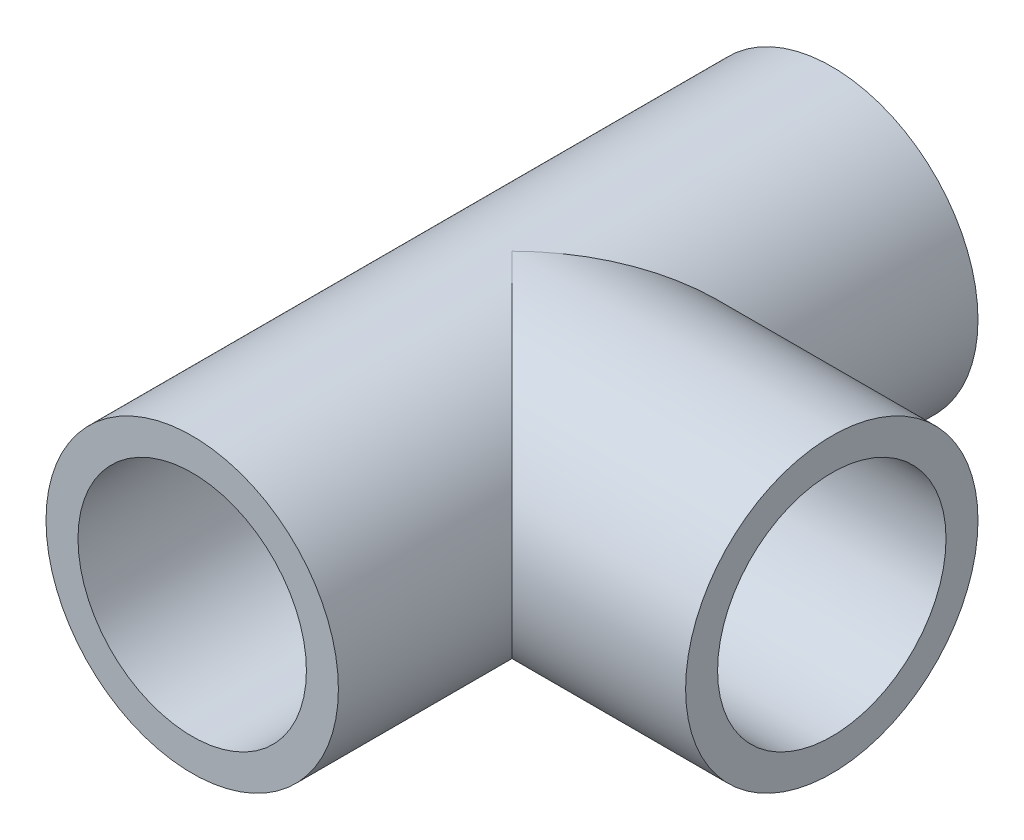
SolidWorks part; units mm, degrees
ref_plane "前视基准面" through (0, 0, 0) normal (0, 0, 1) x (1, 0, 0)
ref_plane "上视基准面" through (0, 0, 0) normal (0, 1, 0) x (1, 0, 0)
ref_plane "右视基准面" through (0, 0, 0) normal (1, 0, 0) x (0, 0, -1)
other "Configuration Table"
sketch "草图1" plane through (0, 0, 0) normal (0, 0, 1) x (1, 0, 0)
  circle A0 centre (0, 0) radius 12.5
  circle A1 centre (0, 0) radius 16
  dimension "D1" = 25
  dimension "D2" = 32
extrude "凸台-拉伸1" add sketch "草图1" along normal mid plane 70
sketch "草图2" plane through (0, 0, 0) normal (1, 0, 0) x (0, 0, -1)
  circle A0 centre (0, 0) radius 16
  circle A1 centre (0, 0) radius 12.5
  dimension "D1" = 32
  dimension "D2" = 25
extrude "凸台-拉伸2" add sketch "草图2" along normal blind 35
